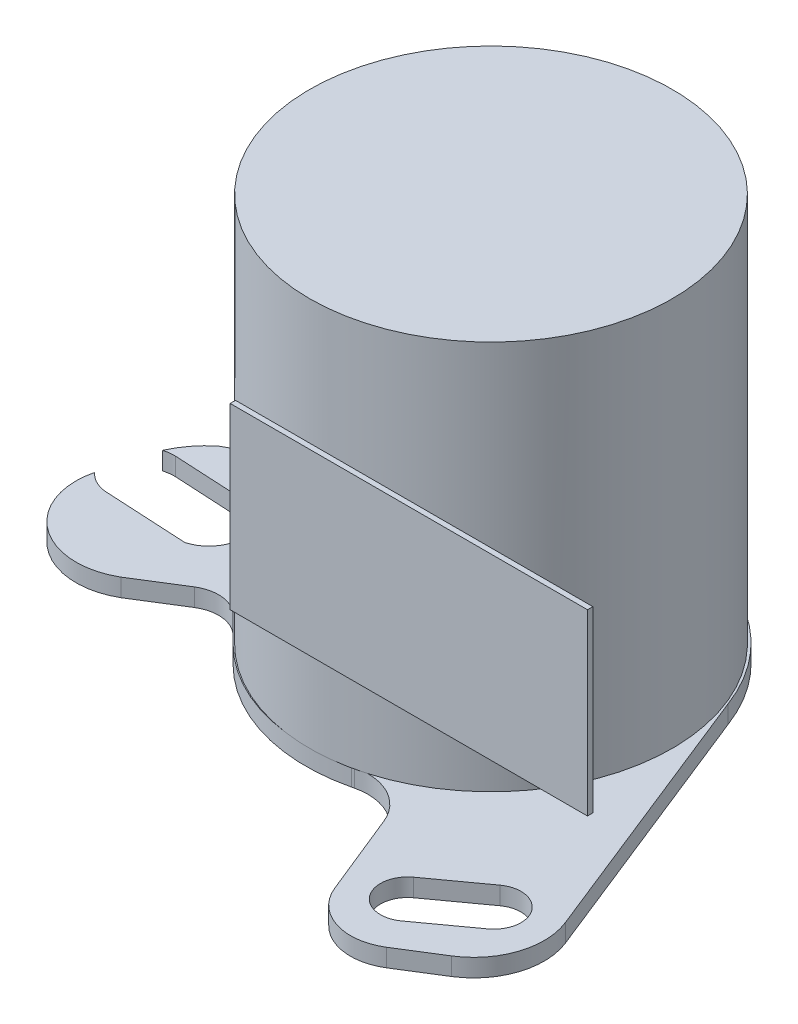
SolidWorks part; units mm, degrees
ref_plane "Front Plane" through (0, 0, 0) normal (0, 0, 1) x (1, 0, 0)
ref_plane "Top Plane" through (0, 0, 0) normal (0, 1, 0) x (1, 0, 0)
ref_plane "Right Plane" through (0, 0, 0) normal (1, 0, 0) x (0, 0, -1)
sketch "Sketch1" plane through (0, 0, 0) normal (0, 1, 0) x (1, 0, 0)
  circle A0 centre (0, 0) radius 5.075
  dimension "D1" = 10.15
extrude "Boss-Extrude1" add sketch "Sketch1" along normal blind 10.9 contours A0
sketch "Sketch2" plane through (0, 0, 0) normal (0, -1, 0) x (1, 0, 0)
  point P0 (7.7389, 6.4247)
  line B0 (4.5762, 6.7384) -> (5.9753, 5.7253)
  line B1 (6.8664, 6.9558) -> (5.4673, 7.9689)
  line B2 (-8.615, -0.9706) -> (-2.3104, -4.5081)
  line B3 (-6.6375, -0.0093) -> (-8.9573, -0.1333)
  line B4 (-9.0556, 1.7057) -> (-6.7358, 1.8297)
  line B5 (-5.5267, 2.7713) -> (-6.797, 3.5644)
  line B6 (-3.6011, 3.6175) -> (-4.3083, 2.9103)
  line B7 (1.0881, 4.9109) -> (1.0174, 4.9277)
  line B8 (3.7414, 8.1191) -> (2.7982, 5.7935)
  line B9 (7.0117, 8.1191) -> (5.8935, 8.8172)
  line B10 (4.771, -1.8673) -> (7.7982, 5.7173)
  arc B11 (5.9753, 5.7253) -> (6.8664, 6.9558) centre (6.4208, 6.3405) ccw
  arc B12 (5.4673, 7.9689) -> (4.5762, 6.7384) centre (5.0217, 7.3536) ccw
  arc B13 (-2.3104, -4.5081) -> (4.771, -1.8673) centre (0.089, -0.1273) ccw
  arc B14 (-9.2857, -0.0912) -> (-8.615, -0.9706) centre (-7.0595, 0.9114) ccw
  arc B15 (-9.2857, -0.0912) -> (-8.9573, -0.1333) centre (-9.0064, 0.7862) ccw
  arc B16 (-6.6375, -0.0093) -> (-6.7358, 1.8297) centre (-7.0009, 0.8934) ccw
  arc B17 (-9.0556, 1.7057) -> (-9.6996, 1.3924) centre (-9.0064, 0.7862) ccw
  arc B18 (-6.797, 3.5644) -> (-9.6996, 1.3924) centre (-7.7837, 1.8575) ccw
  arc B19 (-5.5267, 2.7713) -> (-4.3083, 2.9103) centre (-5.0049, 3.607) ccw
  arc B20 (1.0174, 4.9277) -> (-3.6011, 3.6175) centre (-0.1179, 0.1343) ccw
  arc B21 (1.0881, 4.9109) -> (2.7982, 5.7935) centre (1.4287, 6.3489) ccw
  arc B22 (5.8935, 8.8172) -> (3.7414, 8.1191) centre (5.1109, 7.5637) ccw
  arc B23 (7.7982, 5.7173) -> (7.0117, 8.1191) centre (5.9682, 6.4477) ccw
sketch_block_instance "Block2-1"
sketch_block "Block2"
extrude "Boss-Extrude2" add sketch "Sketch2" along normal blind 0.5
sketch "Sketch3" plane through (0, -0.5, 0) normal (0, -1, 0) x (-1, 0, 0)
  circle A0 centre (0, 0) radius 2.5
  dimension "D1" = 5
extrude "Boss-Extrude3" add sketch "Sketch3" along normal blind 1
sketch "Sketch5" plane through (0, -1.5, 0) normal (0, -1, 0) x (1, 0, 0)
  circle A0 centre (0, 0) radius 0.75
  dimension "D1" = 1.5
extrude "Boss-Extrude4" add sketch "Sketch5" along normal blind 3.4
ref_plane "Plane2" through (0, -3.4, 0) normal (0, -1, 0) x (-1, 0, 0)
sketch "Sketch6" plane through (0, -3.4, 0) normal (0, -1, 0) x (1, 0, 0)
  line L0 (0, 1.675) -> (-0.35, 1.1478)
  line L1 (0, 1.675) -> (0.35, 1.1478)
  line L2 (0.9845, 1.3551) -> (0.3915, 1.1343)
  line L3 (0, 1.2) -> (0, 1.675) construction
  line L4 (0.9845, 1.3551) -> (0.9578, 0.7229)
  line L5 (1.593, 0.5176) -> (0.9835, 0.6876)
  line L6 (1.593, 0.5176) -> (1.1998, 0.0218)
  line L7 (1.593, -0.5176) -> (1.1998, -0.0218)
  line L8 (1.593, -0.5176) -> (0.9835, -0.6876)
  line L9 (0.9845, -1.3551) -> (0.9578, -0.7229)
  line L10 (0.9845, -1.3551) -> (0.3915, -1.1343)
  line L11 (0, -1.675) -> (0.35, -1.1478)
  line L12 (0, -1.675) -> (-0.35, -1.1478)
  line L13 (-0.9845, -1.3551) -> (-0.3915, -1.1343)
  line L14 (-0.9845, -1.3551) -> (-0.9578, -0.7229)
  line L15 (-1.593, -0.5176) -> (-0.9835, -0.6876)
  line L16 (-1.593, -0.5176) -> (-1.1998, -0.0218)
  line L17 (-1.593, 0.5176) -> (-1.1998, 0.0218)
  line L18 (-1.593, 0.5176) -> (-0.9835, 0.6876)
  line L19 (-0.9845, 1.3551) -> (-0.9578, 0.7229)
  line L20 (-0.9845, 1.3551) -> (-0.3915, 1.1343)
  circle A0 centre (0, 0) radius 1.675 construction
  arc A1 (-0.3915, -1.1343) -> (-0.35, -1.1478) centre (0, 0) ccw construction
  arc A2 (-0.3915, -1.1343) -> (-0.35, -1.1478) centre (0, 0) ccw
  arc A3 (-0.9835, -0.6876) -> (-0.9578, -0.7229) centre (0, 0) ccw construction
  arc A4 (-0.9835, -0.6876) -> (-0.9578, -0.7229) centre (0, 0) ccw
  arc A5 (-1.1998, 0.0218) -> (-1.1998, -0.0218) centre (0, 0) ccw construction
  arc A6 (-1.1998, 0.0218) -> (-1.1998, -0.0218) centre (0, 0) ccw
  arc A7 (-0.9578, 0.7229) -> (-0.9835, 0.6876) centre (0, 0) ccw construction
  arc A8 (-0.9578, 0.7229) -> (-0.9835, 0.6876) centre (0, 0) ccw
  arc A9 (-0.35, 1.1478) -> (-0.3915, 1.1343) centre (0, 0) ccw construction
  arc A10 (-0.35, 1.1478) -> (-0.3915, 1.1343) centre (0, 0) ccw
  arc A11 (0.3915, 1.1343) -> (0.35, 1.1478) centre (0, 0) ccw construction
  arc A12 (0.3915, 1.1343) -> (0.35, 1.1478) centre (0, 0) ccw
  arc A13 (0.9835, 0.6876) -> (0.9578, 0.7229) centre (0, 0) ccw construction
  arc A14 (0.9835, 0.6876) -> (0.9578, 0.7229) centre (0, 0) ccw
  arc A15 (1.1998, -0.0218) -> (1.1998, 0.0218) centre (0, 0) ccw construction
  arc A16 (1.1998, -0.0218) -> (1.1998, 0.0218) centre (0, 0) ccw
  arc A17 (0.9578, -0.7229) -> (0.9835, -0.6876) centre (0, 0) ccw construction
  arc A18 (0.9578, -0.7229) -> (0.9835, -0.6876) centre (0, 0) ccw
  arc A19 (0.35, -1.1478) -> (0.3915, -1.1343) centre (0, 0) ccw construction
  arc A20 (0.35, -1.1478) -> (0.3915, -1.1343) centre (0, 0) ccw
  point P37 (0, 0)
  dimension "D1" = 3.35
  dimension "D2" = 2.4
  dimension "D3" = 0.7
  dimension "D4" = 10
extrude "Boss-Extrude5" add sketch "Sketch6" against normal blind 2
ref_plane "Plane3" through (0, 0, 5.075) normal (0, 0, 1) x (1, 0, 0)
sketch "Sketch8" plane through (0, 0, 5.075) normal (0, 0, 1) x (1, 0, 0)
  line L0 (-0.7365, 0) -> (-3.6011, 0) construction
  line L1 (7.925, 7.4) -> (-2.075, 7.4)
  line L2 (7.925, 7.4) -> (7.925, 2.4)
  line L3 (7.925, 2.4) -> (-2.075, 2.4)
  line L4 (-2.075, 7.4) -> (-2.075, 2.4)
  line L5 (-5.075, 10.9) -> (-5.075, 0) construction
  dimension "D1" = 2.4
  dimension "D2" = 5
  dimension "D3" = 10
  dimension "D4" = 5
  dimension "D5" = 3
extrude "Boss-Extrude6" add sketch "Sketch8" along normal blind 0.15 separate body
